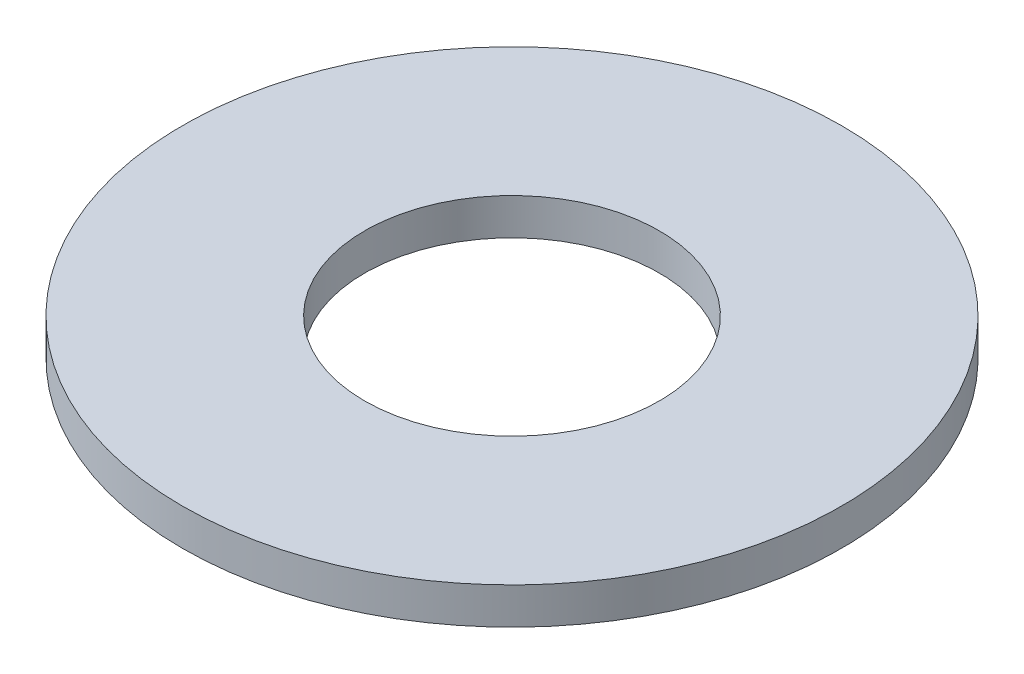
SolidWorks part; units mm, degrees
ref_plane "Front Plane" through (0, 0, 0) normal (0, 0, 1) x (1, 0, 0)
ref_plane "Top Plane" through (0, 0, 0) normal (0, 1, 0) x (1, 0, 0)
ref_plane "Right Plane" through (0, 0, 0) normal (1, 0, 0) x (0, 0, -1)
sketch "Sketch1" plane through (0, 0, 0) normal (0, 1, 0) x (1, 0, 0)
  circle A0 centre (0, 0) radius 4.025
  circle A1 centre (0, 0) radius 9
  dimension "D1" = 8.05
  dimension "D2" = 18
extrude "Boss-Extrude1" add sketch "Sketch1" along normal blind 1
